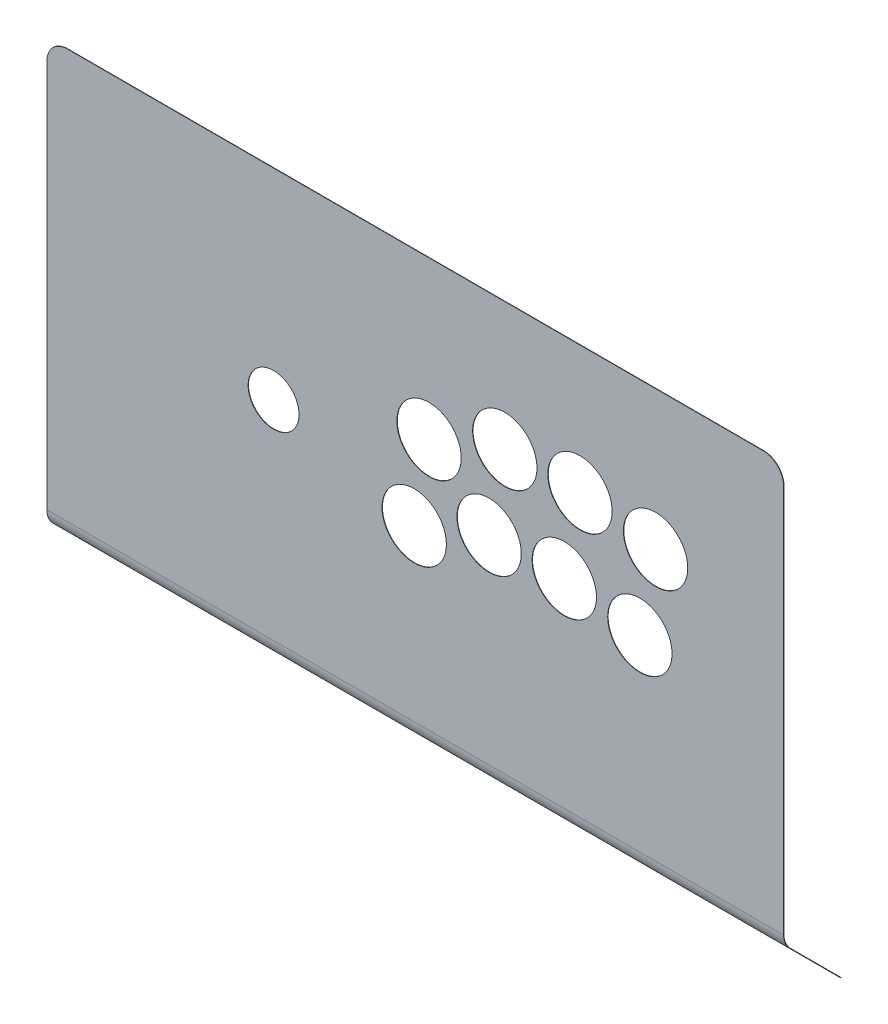
SolidWorks part; units mm, degrees
ref_plane "Alzado" through (0, 0, 0) normal (0, 0, 1) x (1, 0, 0)
ref_plane "Planta" through (0, 0, 0) normal (0, 1, 0) x (1, 0, 0)
ref_plane "Vista lateral" through (0, 0, 0) normal (1, 0, 0) x (0, 0, -1)
sketch "Model" plane through (0, 0, 0) normal (0, 0, 1) x (1, 0, 0)
  line L0 (0, 125) -> (0, -125) construction
  line L1 (-180, 125) -> (180, 125)
  line L2 (-180, 125) -> (-180, -125)
  line L3 (-180, -125) -> (180, -125)
  line L4 (-180, -75) -> (180, -75) construction
  line L5 (180, 125) -> (180, -125)
  spline S0 degree 3 poles (-56.8187, 26.8821) (-56.8187, 33.7469) (-62.3836, 39.3114) (-69.2483, 39.3114) knots 0 0 0 0 1 1 1 1
  spline S1 degree 3 poles (-69.2483, 39.3114) (-76.1131, 39.3114) (-81.6783, 33.7469) (-81.6783, 26.8821) knots 1 1 1 1 2 2 2 2
  spline S2 degree 3 poles (-81.6783, 26.8821) (-81.6783, 20.0173) (-76.1131, 14.4528) (-69.2483, 14.4528) knots 2 2 2 2 3 3 3 3
  spline S3 degree 3 poles (-69.2483, 14.4528) (-62.3836, 14.4528) (-56.8187, 20.0173) (-56.8187, 26.8821) knots 3 3 3 3 4 4 4 4
  spline S4 degree 3 poles (59.4626, 62.4254) (59.4626, 71.1026) (52.4291, 78.1364) (43.7516, 78.1364) knots 0 0 0 0 1 1 1 1
  spline S5 degree 3 poles (43.7516, 78.1364) (35.0748, 78.1364) (28.0402, 71.1026) (28.0402, 62.4254) knots 1 1 1 1 2 2 2 2
  spline S6 degree 3 poles (28.0402, 62.4254) (28.0402, 53.7483) (35.0748, 46.7144) (43.7516, 46.7144) knots 2 2 2 2 3 3 3 3
  spline S7 degree 3 poles (43.7516, 46.7144) (52.4291, 46.7144) (59.4626, 53.7483) (59.4626, 62.4254) knots 3 3 3 3 4 4 4 4
  spline S8 degree 3 poles (96.199, 62.4254) (96.199, 71.1026) (89.1651, 78.1364) (80.488, 78.1364) knots 0 0 0 0 1 1 1 1
  spline S9 degree 3 poles (80.488, 78.1364) (71.8115, 78.1364) (64.7772, 71.1026) (64.7772, 62.4254) knots 1 1 1 1 2 2 2 2
  spline S10 degree 3 poles (64.7772, 62.4254) (64.7772, 53.7483) (71.8115, 46.7144) (80.488, 46.7144) knots 2 2 2 2 3 3 3 3
  spline S11 degree 3 poles (80.488, 46.7144) (89.1651, 46.7144) (96.199, 53.7483) (96.199, 62.4254) knots 3 3 3 3 4 4 4 4
  spline S12 degree 3 poles (133.1329, 56.9314) (133.1329, 65.6086) (126.099, 72.6424) (117.4219, 72.6424) knots 0 0 0 0 1 1 1 1
  spline S13 degree 3 poles (117.4219, 72.6424) (108.7447, 72.6424) (101.7108, 65.6086) (101.7108, 56.9314) knots 1 1 1 1 2 2 2 2
  spline S14 degree 3 poles (101.7108, 56.9314) (101.7108, 48.2542) (108.7447, 41.2203) (117.4219, 41.2203) knots 2 2 2 2 3 3 3 3
  spline S15 degree 3 poles (117.4219, 41.2203) (126.099, 41.2203) (133.1329, 48.2542) (133.1329, 56.9314) knots 3 3 3 3 4 4 4 4
  spline S16 degree 3 poles (125.465, 16.7739) (125.465, 25.4518) (118.4311, 32.4857) (109.754, 32.4857) knots 0 0 0 0 1 1 1 1
  spline S17 degree 3 poles (109.754, 32.4857) (101.0768, 32.4857) (94.0429, 25.4518) (94.0429, 16.7739) knots 1 1 1 1 2 2 2 2
  spline S18 degree 3 poles (94.0429, 16.7739) (94.0429, 8.0974) (101.0768, 1.0636) (109.754, 1.0636) knots 2 2 2 2 3 3 3 3
  spline S19 degree 3 poles (109.754, 1.0636) (118.4311, 1.0636) (125.465, 8.0974) (125.465, 16.7739) knots 3 3 3 3 4 4 4 4
  spline S20 degree 3 poles (88.5324, 22.2693) (88.5324, 30.9465) (81.4982, 37.9803) (72.8214, 37.9803) knots 0 0 0 0 1 1 1 1
  spline S21 degree 3 poles (72.8214, 37.9803) (64.1439, 37.9803) (57.11, 30.9465) (57.11, 22.2693) knots 1 1 1 1 2 2 2 2
  spline S22 degree 3 poles (57.11, 22.2693) (57.11, 13.5922) (64.1439, 6.5583) (72.8214, 6.5583) knots 2 2 2 2 3 3 3 3
  spline S23 degree 3 poles (72.8214, 6.5583) (81.4982, 6.5583) (88.5324, 13.5922) (88.5324, 22.2693) knots 3 3 3 3 4 4 4 4
  spline S24 degree 3 poles (51.7947, 22.2693) (51.7947, 30.9465) (44.7612, 37.9803) (36.0837, 37.9803) knots 0 0 0 0 1 1 1 1
  spline S25 degree 3 poles (36.0837, 37.9803) (27.4068, 37.9803) (20.3723, 30.9465) (20.3723, 22.2693) knots 1 1 1 1 2 2 2 2
  spline S26 degree 3 poles (20.3723, 22.2693) (20.3723, 13.5922) (27.4068, 6.5583) (36.0837, 6.5583) knots 2 2 2 2 3 3 3 3
  spline S27 degree 3 poles (36.0837, 6.5583) (44.7612, 6.5583) (51.7947, 13.5922) (51.7947, 22.2693) knots 3 3 3 3 4 4 4 4
  spline S28 degree 3 poles (15.1939, 7.9564) (15.1939, 16.6336) (8.16, 23.6675) (-0.5165, 23.6675) knots 0 0 0 0 1 1 1 1
  spline S29 degree 3 poles (-0.5165, 23.6675) (-9.1943, 23.6675) (-16.2282, 16.6336) (-16.2282, 7.9564) knots 1 1 1 1 2 2 2 2
  spline S30 degree 3 poles (-16.2282, 7.9564) (-16.2282, -0.7201) (-9.1943, -7.7539) (-0.5165, -7.7539) knots 2 2 2 2 3 3 3 3
  spline S31 degree 3 poles (-0.5165, -7.7539) (8.16, -7.7539) (15.1939, -0.7201) (15.1939, 7.9564) knots 3 3 3 3 4 4 4 4
  spline S32 degree 3 poles (22.4455, 48.1132) (22.4455, 56.7897) (15.412, 63.8242) (6.7352, 63.8242) knots 0 0 0 0 1 1 1 1
  spline S33 degree 3 poles (6.7352, 63.8242) (-1.942, 63.8242) (-8.9762, 56.7897) (-8.9762, 48.1132) knots 1 1 1 1 2 2 2 2
  spline S34 degree 3 poles (-8.9762, 48.1132) (-8.9762, 39.436) (-1.942, 32.4021) (6.7352, 32.4021) knots 2 2 2 2 3 3 3 3
  spline S35 degree 3 poles (6.7352, 32.4021) (15.412, 32.4021) (22.4455, 39.436) (22.4455, 48.1132) knots 3 3 3 3 4 4 4 4
  dimension "D1" = 360
  dimension "D2" = 250
sketch "Croquis1" plane through (0, 0, 0) normal (1, 0, 0) x (0, 0, -1)
  line L0 (0, 0) -> (0, -200) construction
  line L10 (0, -200) -> (-10, -200) construction
  line L11 (0, -200) -> (10, -200) construction
  line L12 (10, -200) -> (10, -210) construction
  line L13 (10, -200) -> (50.251, -240.251) construction
  line L14 (2.9289, -207.0711) -> (32.7307, -236.8728) construction
  line L15 (10, -200) -> (2.9289, -207.0711) construction
  line L21 (-0.1, 0) -> (-0.1, -200)
  line L22 (2.8582, -207.1418) -> (32.6599, -236.9435)
  line L23 (0.1, 0) -> (0.1, -200)
  line L24 (2.9996, -207.0004) -> (32.8014, -236.8021)
  line L25 (-0.1, 0) -> (0.1, 0)
  line L26 (32.6599, -236.9435) -> (32.8014, -236.8021)
  arc A0 (0, -200) -> (2.9289, -207.0711) centre (10, -200) ccw construction
  arc A4 (-0.1, -200) -> (2.8582, -207.1418) centre (10, -200) ccw
  arc A5 (0.1, -200) -> (2.9996, -207.0004) centre (10, -200) ccw
  dimension "D1" = 45
  dimension "D2" = 45
extrude "Saliente-Extruir1" add sketch "Croquis1" along normal mid plane 360
sketch "Croquis3" plane through (0, 0, 0.1) normal (0, 0, 1) x (1, 0, 0)
  line L0 (0, 0) -> (0, -250) construction
  line L1 (-180, 0) -> (180, 0) construction
  line L2 (-180, 0) -> (-180, -250) construction
  line L3 (-180, -250) -> (180, -250) construction
  line L4 (-180, -200) -> (180, -200) construction
  line L5 (180, 0) -> (180, -250) construction
  spline S0 degree 3 poles (-56.8187, -98.1179) (-56.8187, -91.2531) (-62.3836, -85.6886) (-69.2483, -85.6886) knots 0 0 0 0 1 1 1 1
  spline S1 degree 3 poles (-69.2483, -85.6886) (-76.1131, -85.6886) (-81.6783, -91.2531) (-81.6783, -98.1179) knots 1 1 1 1 2 2 2 2
  spline S2 degree 3 poles (-81.6783, -98.1179) (-81.6783, -104.9827) (-76.1131, -110.5472) (-69.2483, -110.5472) knots 2 2 2 2 3 3 3 3
  spline S3 degree 3 poles (-69.2483, -110.5472) (-62.3836, -110.5472) (-56.8187, -104.9827) (-56.8187, -98.1179) knots 3 3 3 3 4 4 4 4
  spline S4 degree 3 poles (59.4626, -62.5746) (59.4626, -53.8974) (52.4291, -46.8636) (43.7516, -46.8636) knots 0 0 0 0 1 1 1 1
  spline S5 degree 3 poles (43.7516, -46.8636) (35.0748, -46.8636) (28.0402, -53.8974) (28.0402, -62.5746) knots 1 1 1 1 2 2 2 2
  spline S6 degree 3 poles (28.0402, -62.5746) (28.0402, -71.2517) (35.0748, -78.2856) (43.7516, -78.2856) knots 2 2 2 2 3 3 3 3
  spline S7 degree 3 poles (43.7516, -78.2856) (52.4291, -78.2856) (59.4626, -71.2517) (59.4626, -62.5746) knots 3 3 3 3 4 4 4 4
  spline S8 degree 3 poles (96.199, -62.5746) (96.199, -53.8974) (89.1651, -46.8636) (80.488, -46.8636) knots 0 0 0 0 1 1 1 1
  spline S9 degree 3 poles (80.488, -46.8636) (71.8115, -46.8636) (64.7772, -53.8974) (64.7772, -62.5746) knots 1 1 1 1 2 2 2 2
  spline S10 degree 3 poles (64.7772, -62.5746) (64.7772, -71.2517) (71.8115, -78.2856) (80.488, -78.2856) knots 2 2 2 2 3 3 3 3
  spline S11 degree 3 poles (80.488, -78.2856) (89.1651, -78.2856) (96.199, -71.2517) (96.199, -62.5746) knots 3 3 3 3 4 4 4 4
  spline S12 degree 3 poles (133.1329, -68.0686) (133.1329, -59.3914) (126.099, -52.3576) (117.4219, -52.3576) knots 0 0 0 0 1 1 1 1
  spline S13 degree 3 poles (117.4219, -52.3576) (108.7447, -52.3576) (101.7108, -59.3914) (101.7108, -68.0686) knots 1 1 1 1 2 2 2 2
  spline S14 degree 3 poles (101.7108, -68.0686) (101.7108, -76.7458) (108.7447, -83.7797) (117.4219, -83.7797) knots 2 2 2 2 3 3 3 3
  spline S15 degree 3 poles (117.4219, -83.7797) (126.099, -83.7797) (133.1329, -76.7458) (133.1329, -68.0686) knots 3 3 3 3 4 4 4 4
  spline S16 degree 3 poles (125.465, -108.2261) (125.465, -99.5482) (118.4311, -92.5143) (109.754, -92.5143) knots 0 0 0 0 1 1 1 1
  spline S17 degree 3 poles (109.754, -92.5143) (101.0768, -92.5143) (94.0429, -99.5482) (94.0429, -108.2261) knots 1 1 1 1 2 2 2 2
  spline S18 degree 3 poles (94.0429, -108.2261) (94.0429, -116.9026) (101.0768, -123.9364) (109.754, -123.9364) knots 2 2 2 2 3 3 3 3
  spline S19 degree 3 poles (109.754, -123.9364) (118.4311, -123.9364) (125.465, -116.9026) (125.465, -108.2261) knots 3 3 3 3 4 4 4 4
  spline S20 degree 3 poles (88.5324, -102.7307) (88.5324, -94.0535) (81.4982, -87.0197) (72.8214, -87.0197) knots 0 0 0 0 1 1 1 1
  spline S21 degree 3 poles (72.8214, -87.0197) (64.1439, -87.0197) (57.11, -94.0535) (57.11, -102.7307) knots 1 1 1 1 2 2 2 2
  spline S22 degree 3 poles (57.11, -102.7307) (57.11, -111.4078) (64.1439, -118.4417) (72.8214, -118.4417) knots 2 2 2 2 3 3 3 3
  spline S23 degree 3 poles (72.8214, -118.4417) (81.4982, -118.4417) (88.5324, -111.4078) (88.5324, -102.7307) knots 3 3 3 3 4 4 4 4
  spline S24 degree 3 poles (51.7947, -102.7307) (51.7947, -94.0535) (44.7612, -87.0197) (36.0837, -87.0197) knots 0 0 0 0 1 1 1 1
  spline S25 degree 3 poles (36.0837, -87.0197) (27.4068, -87.0197) (20.3723, -94.0535) (20.3723, -102.7307) knots 1 1 1 1 2 2 2 2
  spline S26 degree 3 poles (20.3723, -102.7307) (20.3723, -111.4078) (27.4068, -118.4417) (36.0837, -118.4417) knots 2 2 2 2 3 3 3 3
  spline S27 degree 3 poles (36.0837, -118.4417) (44.7612, -118.4417) (51.7947, -111.4078) (51.7947, -102.7307) knots 3 3 3 3 4 4 4 4
  spline S28 degree 3 poles (15.1939, -117.0436) (15.1939, -108.3664) (8.16, -101.3325) (-0.5165, -101.3325) knots 0 0 0 0 1 1 1 1
  spline S29 degree 3 poles (-0.5165, -101.3325) (-9.1943, -101.3325) (-16.2282, -108.3664) (-16.2282, -117.0436) knots 1 1 1 1 2 2 2 2
  spline S30 degree 3 poles (-16.2282, -117.0436) (-16.2282, -125.7201) (-9.1943, -132.7539) (-0.5165, -132.7539) knots 2 2 2 2 3 3 3 3
  spline S31 degree 3 poles (-0.5165, -132.7539) (8.16, -132.7539) (15.1939, -125.7201) (15.1939, -117.0436) knots 3 3 3 3 4 4 4 4
  spline S32 degree 3 poles (22.4455, -76.8868) (22.4455, -68.2103) (15.412, -61.1758) (6.7352, -61.1758) knots 0 0 0 0 1 1 1 1
  spline S33 degree 3 poles (6.7352, -61.1758) (-1.942, -61.1758) (-8.9762, -68.2103) (-8.9762, -76.8868) knots 1 1 1 1 2 2 2 2
  spline S34 degree 3 poles (-8.9762, -76.8868) (-8.9762, -85.564) (-1.942, -92.5979) (6.7352, -92.5979) knots 2 2 2 2 3 3 3 3
  spline S35 degree 3 poles (6.7352, -92.5979) (15.412, -92.5979) (22.4455, -85.564) (22.4455, -76.8868) knots 3 3 3 3 4 4 4 4
  dimension "D1" = 250
extrude "Cortar-Extruir1" cut sketch "Croquis3" against normal through all
fillet "Redondeo1" radius 10 4 edges at (-180, 0, 0) (180, 0, 0) (180, -236.8728, -32.7307) (-180, -236.8728, -32.7307)
